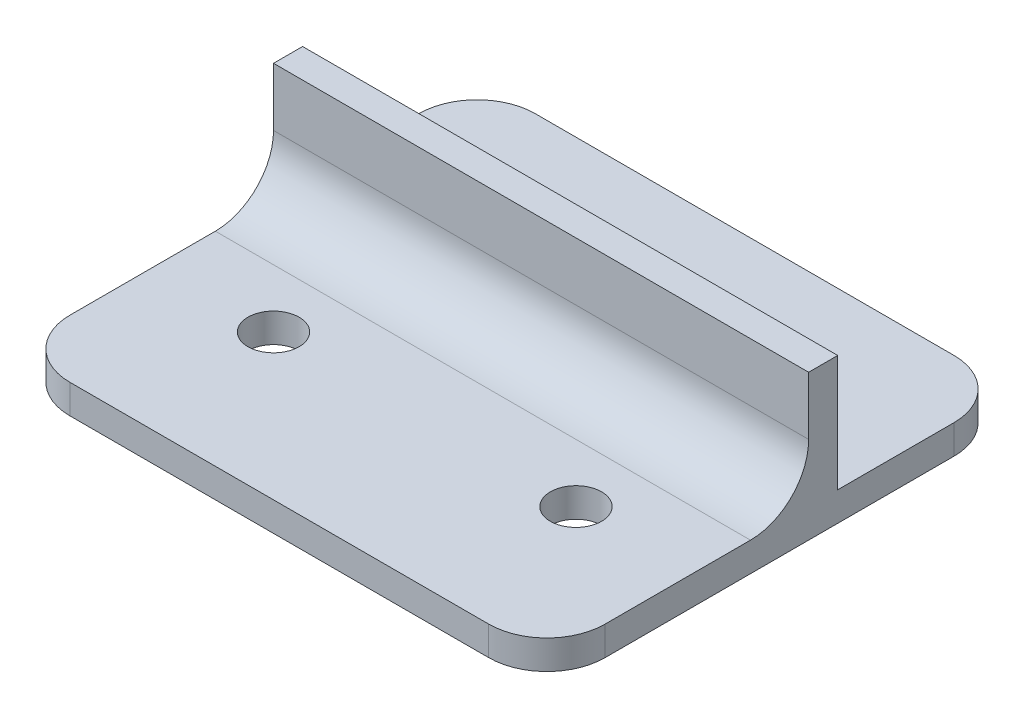
SolidWorks part; units mm, degrees
ref_plane "Front Plane" through (0, 0, 0) normal (0, 0, 1) x (1, 0, 0)
ref_plane "Top Plane" through (0, 0, 0) normal (0, 1, 0) x (1, 0, 0)
ref_plane "Right Plane" through (0, 0, 0) normal (1, 0, 0) x (0, 0, -1)
sketch "Sketch1" plane through (0, 0, 0) normal (0, 1, 0) x (1, 0, 0)
  line L0 (-26, 40) -> (-26, -40) construction
  line L1 (-36, 40) -> (36, 40)
  line L2 (-46, 30) -> (-46, -30)
  line L3 (-36, -40) -> (36, -40)
  line L4 (46, 30) -> (46, -30)
  line L5 (-46, 40) -> (46, -40) construction
  line L6 (-46, -40) -> (46, 40) construction
  line L7 (26, 40) -> (26, -40) construction
  line L8 (-46, 10) -> (46, 10) construction
  line L9 (-46, 24) -> (46, 24) construction
  line L10 (-46, -15) -> (46, -15) construction
  circle A2 centre (-26, -15) radius 4.4
  circle A3 centre (26, -15) radius 4.4
  arc A4 (46, 30) -> (36, 40) centre (36, 30) ccw
  arc A5 (-36, 40) -> (-46, 30) centre (-36, 30) ccw
  arc A6 (36, -40) -> (46, -30) centre (36, -30) ccw
  arc A7 (-36, -40) -> (-46, -30) centre (-36, -30) cw
  point P0 (0, 0)
  dimension "D7" = 25
  dimension "D8" = 10
  dimension "D1" = 80
  dimension "D2" = 92
  dimension "D3" = 20
  dimension "D4" = 20
  dimension "D5" = 30
  dimension "D6" = 14
extrude "Boss-Extrude1" add sketch "Sketch1" against normal blind 5
sketch "Sketch2" plane through (0, 0, 0) normal (0, 1, 0) x (1, 0, 0)
  line L0 (-46, 10) -> (46, 10)
  line L1 (-46, 30) -> (-46, -30) construction
  line L2 (46, -30) -> (46, 30) construction
  line L3 (36, 40) -> (-36, 40) construction
  line L4 (-46, 10) -> (-46, 5)
  line L5 (-46, 5) -> (46, 5)
  line L6 (46, 5) -> (46, 10)
  dimension "D1" = 30
  dimension "D2" = 5
extrude "Boss-Extrude2" add sketch "Sketch2" along normal blind 20
fillet "Fillet1" radius 10 1 edges at (0, 0, -5)
sketch "Sketch3" plane through (0, -5, 0) normal (0, -1, 0) x (1, 0, 0)
  circle A0 centre (-26, -24) radius 5
  circle A1 centre (26, -24) radius 5
extrude "Cut-Extrude1" cut sketch "Sketch3" against normal up to surface (5 mm away) draft 24 up to face at (0, 0, -27.357)
